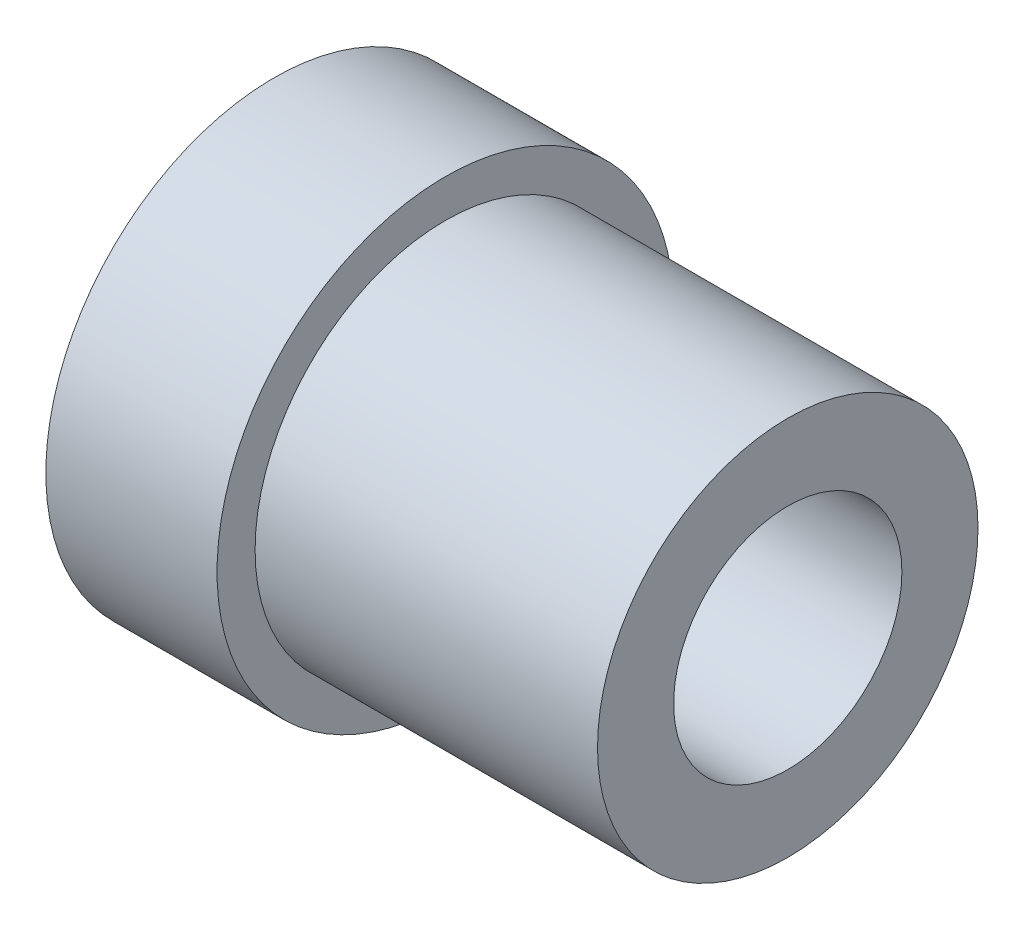
SolidWorks part; units mm, degrees
ref_plane "Front Plane" through (0, 0, 0) normal (0, 0, 1) x (1, 0, 0)
ref_plane "Top Plane" through (0, 0, 0) normal (0, 1, 0) x (1, 0, 0)
ref_plane "Right Plane" through (0, 0, 0) normal (1, 0, 0) x (0, 0, -1)
sketch "Sketch1" plane through (0, 0, 0) normal (1, 0, 0) x (0, 0, -1)
  circle A0 centre (0, 0) radius 3
  circle A1 centre (0, 0) radius 6
  dimension "D1" = 12
  dimension "D2" = 6
extrude "Boss-Extrude1" add sketch "Sketch1" along normal blind 4.5
sketch "Sketch2" plane through (4.5, 0, 0) normal (1, 0, 0) x (0, 0, -1)
  circle A0 centre (0, 0) radius 3 construction
  circle A1 centre (0, 0) radius 3
  circle A2 centre (0, 0) radius 5
  dimension "D1" = 10
extrude "Boss-Extrude2" add sketch "Sketch2" along normal blind 9
